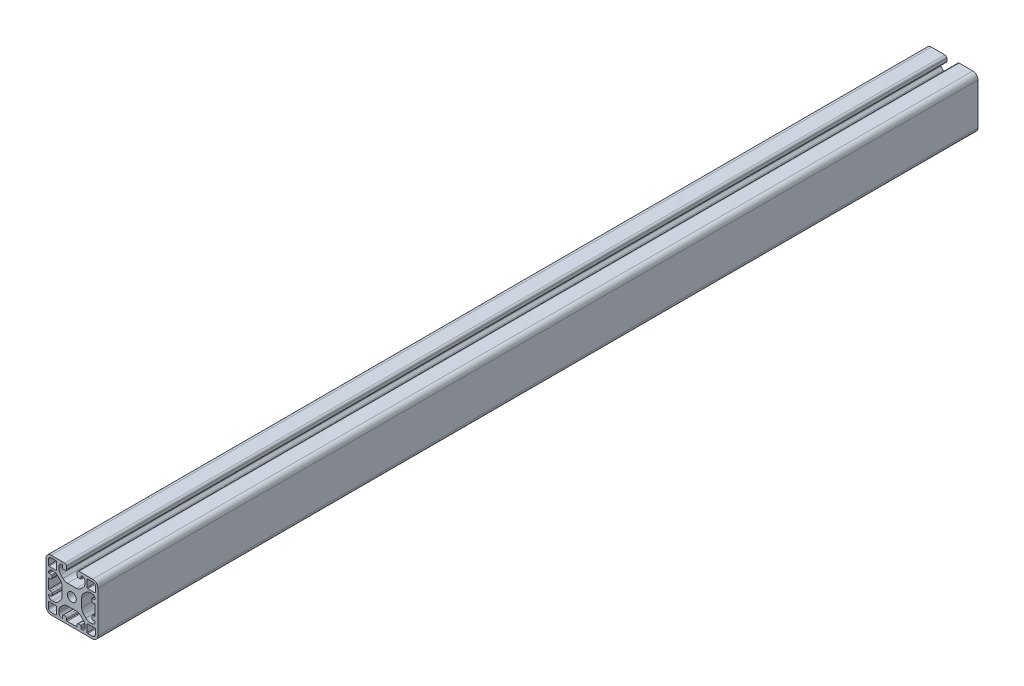
SolidWorks part; units mm, degrees
ref_plane "Ebene vorne" through (0, 0, 0) normal (0, 0, 1) x (1, 0, 0)
ref_plane "Ebene oben" through (0, 0, 0) normal (0, 1, 0) x (1, 0, 0)
ref_plane "Ebene rechts" through (0, 0, 0) normal (1, 0, 0) x (0, 0, -1)
ref_plane "Ebene1" through (0, 0, 680) normal (0, 0, 1) x (1, 0, 0)
sketch "Skizze1" plane through (0, 0, 680) normal (0, 0, 1) x (1, 0, 0)
  line L0 (0, 38.2) -> (3.7, 38.2)
  line L1 (4.2, 37.7) -> (4.2, 32.3)
  line L2 (3.7, 31.8) -> (-1.7, 31.8)
  line L3 (-2.2, 32.3) -> (-2.2, 36)
  line L4 (-2.2, 4) -> (-2.2, 7.7)
  line L5 (-1.7, 8.2) -> (3.7, 8.2)
  line L6 (4.2, 7.7) -> (4.2, 2.3)
  line L7 (3.7, 1.8) -> (0, 1.8)
  line L8 (32, 1.8) -> (28.3, 1.8)
  line L9 (27.8, 2.3) -> (27.8, 7.7)
  line L10 (28.3, 8.2) -> (33.7, 8.2)
  line L11 (34.2, 7.7) -> (34.2, 4)
  line L12 (34.2, 36) -> (34.2, 32.3)
  line L13 (33.7, 31.8) -> (28.3, 31.8)
  line L14 (27.8, 32.3) -> (27.8, 37.7)
  line L15 (28.3, 38.2) -> (32, 38.2)
  line L16 (12.5924, 12.4) -> (19.4076, 12.4)
  line L17 (22.9431, 10.9355) -> (24.6355, 9.2431)
  line L18 (26.1, 5.7076) -> (26.1, 4.5)
  line L19 (23.1, 2.5) -> (23.1, 4.15)
  line L20 (22.6, 4.65) -> (21.1, 4.65)
  line L21 (20.1, 3.65) -> (20.1, 2.5)
  line L22 (19.6, 2) -> (12.4, 2)
  line L23 (11.9, 2.5) -> (11.9, 3.65)
  line L24 (10.9, 4.65) -> (9.4, 4.65)
  line L25 (8.9, 4.15) -> (8.9, 2.5)
  line L26 (5.9, 4.5) -> (5.9, 5.7076)
  line L27 (7.3645, 9.2431) -> (9.0569, 10.9355)
  line L28 (-0.35, 15.9) -> (-1.5, 15.9)
  line L29 (-2, 16.4) -> (-2, 23.6)
  line L30 (-1.5, 24.1) -> (-0.35, 24.1)
  line L31 (0.65, 25.1) -> (0.65, 26.6)
  line L32 (0.15, 27.1) -> (-1.5, 27.1)
  line L33 (0.5, 30.1) -> (1.7076, 30.1)
  line L34 (5.2431, 28.6355) -> (6.9355, 26.9431)
  line L35 (8.4, 23.4076) -> (8.4, 16.5924)
  line L36 (6.9355, 13.0569) -> (5.2431, 11.3645)
  line L37 (1.7076, 9.9) -> (0.5, 9.9)
  line L38 (-1.5, 12.9) -> (0.15, 12.9)
  line L39 (0.65, 13.4) -> (0.65, 14.9)
  line L40 (23.6, 16.5924) -> (23.6, 23.4076)
  line L41 (25.0645, 26.9431) -> (26.7569, 28.6355)
  line L42 (30.2924, 30.1) -> (31.5, 30.1)
  line L43 (33.5, 27.1) -> (31.85, 27.1)
  line L44 (31.35, 26.6) -> (31.35, 25.1)
  line L45 (32.35, 24.1) -> (33.5, 24.1)
  line L46 (34, 23.6) -> (34, 16.4)
  line L47 (33.5, 15.9) -> (32.35, 15.9)
  line L48 (31.35, 14.9) -> (31.35, 13.4)
  line L49 (31.85, 12.9) -> (33.5, 12.9)
  line L50 (31.5, 9.9) -> (30.2924, 9.9)
  line L51 (26.7569, 11.3645) -> (25.0645, 13.0569)
  line L52 (23.1, 35.85) -> (23.1, 37.5)
  line L53 (26.1, 35.5) -> (26.1, 34.2924)
  line L54 (24.6355, 30.7569) -> (22.9431, 29.0645)
  line L55 (19.4076, 27.6) -> (12.5924, 27.6)
  line L56 (9.0569, 29.0645) -> (7.3645, 30.7569)
  line L57 (5.9, 34.2924) -> (5.9, 35.5)
  line L58 (8.9, 37.5) -> (8.9, 35.85)
  line L59 (9.4, 35.35) -> (10.9, 35.35)
  line L60 (11.9, 36.35) -> (11.9, 38.5)
  line L61 (10.4, 40) -> (0, 40)
  line L62 (-4, 36) -> (-4, 4)
  line L63 (0, 0) -> (32, 0)
  line L64 (36, 4) -> (36, 36)
  line L65 (32, 40) -> (21.6, 40)
  line L66 (20.1, 38.5) -> (20.1, 36.35)
  line L67 (21.1, 35.35) -> (22.6, 35.35)
  circle A0 centre (16, 20) radius 3.4
  arc A1 (3.7, 38.2) -> (4.2, 37.7) centre (3.7, 37.7) cw
  arc A2 (4.2, 32.3) -> (3.7, 31.8) centre (3.7, 32.3) cw
  arc A3 (-1.7, 31.8) -> (-2.2, 32.3) centre (-1.7, 32.3) cw
  arc A4 (-2.2, 36) -> (0, 38.2) centre (0, 36) cw
  arc A5 (-2.2, 7.7) -> (-1.7, 8.2) centre (-1.7, 7.7) cw
  arc A6 (3.7, 8.2) -> (4.2, 7.7) centre (3.7, 7.7) cw
  arc A7 (4.2, 2.3) -> (3.7, 1.8) centre (3.7, 2.3) cw
  arc A8 (0, 1.8) -> (-2.2, 4) centre (0, 4) cw
  arc A9 (28.3, 1.8) -> (27.8, 2.3) centre (28.3, 2.3) cw
  arc A10 (27.8, 7.7) -> (28.3, 8.2) centre (28.3, 7.7) cw
  arc A11 (33.7, 8.2) -> (34.2, 7.7) centre (33.7, 7.7) cw
  arc A12 (34.2, 4) -> (32, 1.8) centre (32, 4) cw
  arc A13 (34.2, 32.3) -> (33.7, 31.8) centre (33.7, 32.3) cw
  arc A14 (28.3, 31.8) -> (27.8, 32.3) centre (28.3, 32.3) cw
  arc A15 (27.8, 37.7) -> (28.3, 38.2) centre (28.3, 37.7) cw
  arc A16 (32, 38.2) -> (34.2, 36) centre (32, 36) cw
  arc A17 (19.4076, 12.4) -> (22.9431, 10.9355) centre (19.4076, 7.4) cw
  arc A18 (24.6355, 9.2431) -> (26.1, 5.7076) centre (21.1, 5.7076) cw
  arc A19 (26.1, 4.5) -> (23.6, 2) centre (23.6, 4.5) cw
  arc A20 (23.6, 2) -> (23.1, 2.5) centre (23.6, 2.5) cw
  arc A21 (23.1, 4.15) -> (22.6, 4.65) centre (22.6, 4.15) ccw
  arc A22 (21.1, 4.65) -> (20.1, 3.65) centre (21.1, 3.65) ccw
  arc A23 (20.1, 2.5) -> (19.6, 2) centre (19.6, 2.5) cw
  arc A24 (12.4, 2) -> (11.9, 2.5) centre (12.4, 2.5) cw
  arc A25 (11.9, 3.65) -> (10.9, 4.65) centre (10.9, 3.65) ccw
  arc A26 (9.4, 4.65) -> (8.9, 4.15) centre (9.4, 4.15) ccw
  arc A27 (8.9, 2.5) -> (8.4, 2) centre (8.4, 2.5) cw
  arc A28 (8.4, 2) -> (5.9, 4.5) centre (8.4, 4.5) cw
  arc A29 (5.9, 5.7076) -> (7.3645, 9.2431) centre (10.9, 5.7076) cw
  arc A30 (9.0569, 10.9355) -> (12.5924, 12.4) centre (12.5924, 7.4) cw
  arc A31 (-1.5, 15.9) -> (-2, 16.4) centre (-1.5, 16.4) cw
  arc A32 (-2, 23.6) -> (-1.5, 24.1) centre (-1.5, 23.6) cw
  arc A33 (-0.35, 24.1) -> (0.65, 25.1) centre (-0.35, 25.1) ccw
  arc A34 (0.65, 26.6) -> (0.15, 27.1) centre (0.15, 26.6) ccw
  arc A35 (-1.5, 27.1) -> (-2, 27.6) centre (-1.5, 27.6) cw
  arc A36 (-2, 27.6) -> (0.5, 30.1) centre (0.5, 27.6) cw
  arc A37 (1.7076, 30.1) -> (5.2431, 28.6355) centre (1.7076, 25.1) cw
  arc A38 (6.9355, 26.9431) -> (8.4, 23.4076) centre (3.4, 23.4076) cw
  arc A39 (8.4, 16.5924) -> (6.9355, 13.0569) centre (3.4, 16.5924) cw
  arc A40 (5.2431, 11.3645) -> (1.7076, 9.9) centre (1.7076, 14.9) cw
  arc A41 (0.5, 9.9) -> (-2, 12.4) centre (0.5, 12.4) cw
  arc A42 (-2, 12.4) -> (-1.5, 12.9) centre (-1.5, 12.4) cw
  arc A43 (0.15, 12.9) -> (0.65, 13.4) centre (0.15, 13.4) ccw
  arc A44 (0.65, 14.9) -> (-0.35, 15.9) centre (-0.35, 14.9) ccw
  arc A45 (23.6, 23.4076) -> (25.0645, 26.9431) centre (28.6, 23.4076) cw
  arc A46 (26.7569, 28.6355) -> (30.2924, 30.1) centre (30.2924, 25.1) cw
  arc A47 (31.5, 30.1) -> (34, 27.6) centre (31.5, 27.6) cw
  arc A48 (34, 27.6) -> (33.5, 27.1) centre (33.5, 27.6) cw
  arc A49 (31.85, 27.1) -> (31.35, 26.6) centre (31.85, 26.6) ccw
  arc A50 (31.35, 25.1) -> (32.35, 24.1) centre (32.35, 25.1) ccw
  arc A51 (33.5, 24.1) -> (34, 23.6) centre (33.5, 23.6) cw
  arc A52 (34, 16.4) -> (33.5, 15.9) centre (33.5, 16.4) cw
  arc A53 (32.35, 15.9) -> (31.35, 14.9) centre (32.35, 14.9) ccw
  arc A54 (31.35, 13.4) -> (31.85, 12.9) centre (31.85, 13.4) ccw
  arc A55 (33.5, 12.9) -> (34, 12.4) centre (33.5, 12.4) cw
  arc A56 (34, 12.4) -> (31.5, 9.9) centre (31.5, 12.4) cw
  arc A57 (30.2924, 9.9) -> (26.7569, 11.3645) centre (30.2924, 14.9) cw
  arc A58 (25.0645, 13.0569) -> (23.6, 16.5924) centre (28.6, 16.5924) cw
  arc A59 (22.6, 35.35) -> (23.1, 35.85) centre (22.6, 35.85) ccw
  arc A60 (23.1, 37.5) -> (23.6, 38) centre (23.6, 37.5) cw
  arc A61 (23.6, 38) -> (26.1, 35.5) centre (23.6, 35.5) cw
  arc A62 (26.1, 34.2924) -> (24.6355, 30.7569) centre (21.1, 34.2924) cw
  arc A63 (22.9431, 29.0645) -> (19.4076, 27.6) centre (19.4076, 32.6) cw
  arc A64 (12.5924, 27.6) -> (9.0569, 29.0645) centre (12.5924, 32.6) cw
  arc A65 (7.3645, 30.7569) -> (5.9, 34.2924) centre (10.9, 34.2924) cw
  arc A66 (5.9, 35.5) -> (8.4, 38) centre (8.4, 35.5) cw
  arc A67 (8.4, 38) -> (8.9, 37.5) centre (8.4, 37.5) cw
  arc A68 (8.9, 35.85) -> (9.4, 35.35) centre (9.4, 35.85) ccw
  arc A69 (10.9, 35.35) -> (11.9, 36.35) centre (10.9, 36.35) ccw
  arc A70 (11.9, 38.5) -> (10.4, 40) centre (10.4, 38.5) ccw
  arc A71 (0, 40) -> (-4, 36) centre (0, 36) ccw
  arc A72 (-4, 4) -> (0, 0) centre (0, 4) ccw
  arc A73 (32, 0) -> (36, 4) centre (32, 4) ccw
  arc A74 (36, 36) -> (32, 40) centre (32, 36) ccw
  arc A75 (21.6, 40) -> (20.1, 38.5) centre (21.6, 38.5) ccw
  arc A76 (20.1, 36.35) -> (21.1, 35.35) centre (21.1, 36.35) ccw
extrude "Aufsatz-Linear austragen1" add sketch "Skizze1" against normal blind 680
